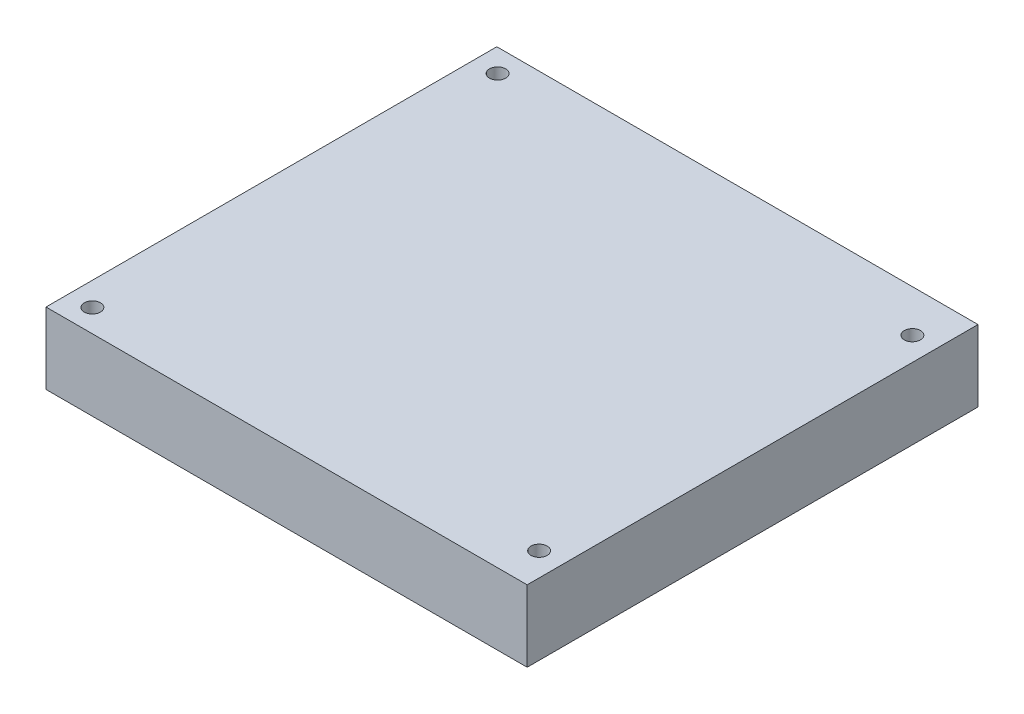
SolidWorks part; units mm, degrees
ref_plane "Front Plane" through (0, 0, 0) normal (0, 0, 1) x (1, 0, 0)
ref_plane "Top Plane" through (0, 0, 0) normal (0, 1, 0) x (1, 0, 0)
ref_plane "Right Plane" through (0, 0, 0) normal (1, 0, 0) x (0, 0, -1)
sketch "Sketch1" plane through (0, 0, 0) normal (0, 1, 0) x (1, 0, 0)
  line L1 (-47.5, -44.505) -> (47.5, -44.505)
  line L2 (-47.5, -44.505) -> (-47.5, 44.505)
  line L3 (-47.5, 44.505) -> (47.5, 44.505)
  line L4 (47.5, -44.505) -> (47.5, 44.505)
  line L5 (-47.5, -44.505) -> (47.5, 44.505) construction
  line L6 (-47.5, 44.505) -> (47.5, -44.505) construction
  circle A0 centre (-42.85, 40) radius 1.6
  circle A1 centre (42.85, 36.2) radius 1.6
  circle A2 centre (-42.85, -40) radius 1.6
  circle A3 centre (42.85, -37.5) radius 1.6
  point P0 (47.5, 44.505)
  point P1 (0, 0)
  point P7 (42.85, 36.2)
  point P8 (42.85, -37.5)
  point P9 (-42.85, 40)
  point P10 (-42.85, -40)
extrude "Boss-Extrude1" add sketch "Sketch1" along normal blind 14.1
